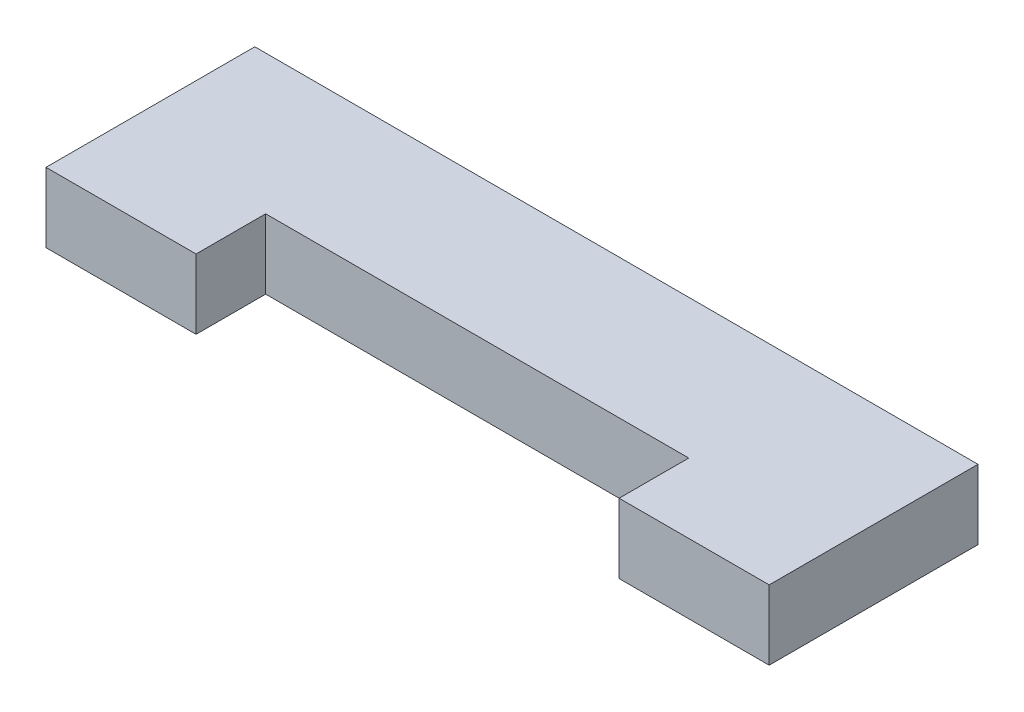
SolidWorks part; units mm, degrees
ref_plane "Front Plane" through (0, 0, 0) normal (0, 0, 1) x (1, 0, 0)
ref_plane "Top Plane" through (0, 0, 0) normal (0, 1, 0) x (1, 0, 0)
ref_plane "Right Plane" through (0, 0, 0) normal (1, 0, 0) x (0, 0, -1)
sketch "Sketch1" plane through (0, 0, 0) normal (0, 1, 0) x (1, 0, 0)
  line L0 (-20, -3.85) -> (-20, -7.7)
  line L1 (-11.7, -3.85) -> (11.7, -3.85)
  line L2 (-20, -3.85) -> (-20, 3.85)
  line L3 (-20, 3.85) -> (20, 3.85)
  line L4 (20, -3.85) -> (20, 3.85)
  line L5 (-20, -3.85) -> (20, 3.85) construction
  line L6 (-20, 3.85) -> (20, -3.85) construction
  line L7 (-20, -7.7) -> (-11.7, -7.7)
  line L8 (-11.7, -7.7) -> (-11.7, -3.85)
  line L9 (0, -55) -> (0, 55) construction
  line L10 (11.7, -7.7) -> (11.7, -3.85)
  line L11 (20, -7.7) -> (11.7, -7.7)
  line L12 (20, -3.85) -> (20, -7.7)
  line L13 (11.7, -3.85) -> (20, -3.85) construction
  line L14 (-20, -3.85) -> (-11.7, -3.85) construction
  point P0 (0, 0)
  dimension "D1" = 7.7
  dimension "D2" = 40
  dimension "D3" = 3.85
  dimension "D4" = 8.3
extrude "Boss-Extrude1" add sketch "Sketch1" along normal blind 3.85
equation "\"m3_hole\"= 3.5"
equation "\"m3_washer\"= 7.3"
equation "\"m3_nut\"= 5.3"
equation "\"plywood_thickness\" = 3.85"
equation "\"guide_width\"= 10.0"
equation "\"guide_length\"= 65.0"
equation "\"guide_tab_length\" = 10.0"
equation "\"guide_tab_width\" = 9.0"
equation "\"guide_thickness\" = 12.0"
equation "\"grinder_od\"= 52.0"
equation "\"grinder_id\"= 45.5"
equation "\"grinder_adjust_od\" = 58.0"
equation "\"funnel_width_from_adjust_ring\" = 13.0"
equation "\"drill_contact_diameter_small\" = 24.0"
equation "\"drill_contact_diameter_medium\" = 28.0"
equation "\"drill_contact_diameter_large\" = 39.0"
equation "\"drill_contact_diameter_tab\" = 31.0"
equation "\"drill_contact_ow_tab\" = 14.5"
equation "\"drill_contact_iw_tab\" = 8.7"
equation "\"drill_contact_small_height\" = 15.5"
equation "\"drill_contact_large_height\" = 34.5"
equation "\"plywood_peg_length\" = 40"
equation "\"plywood_peg_width\" = 8.0"
equation "\"D1@Sketch1\"=\"plywood_thickness\"*2"
equation "\"D2@Sketch1\"=\"plywood_peg_length\""
equation "\"D3@Sketch1\"=\"plywood_thickness\""
equation "\"D4@Sketch1\"=\"plywood_peg_width\"+0.3"
equation "\"D1@Boss-Extrude1\"=\"plywood_thickness\""
